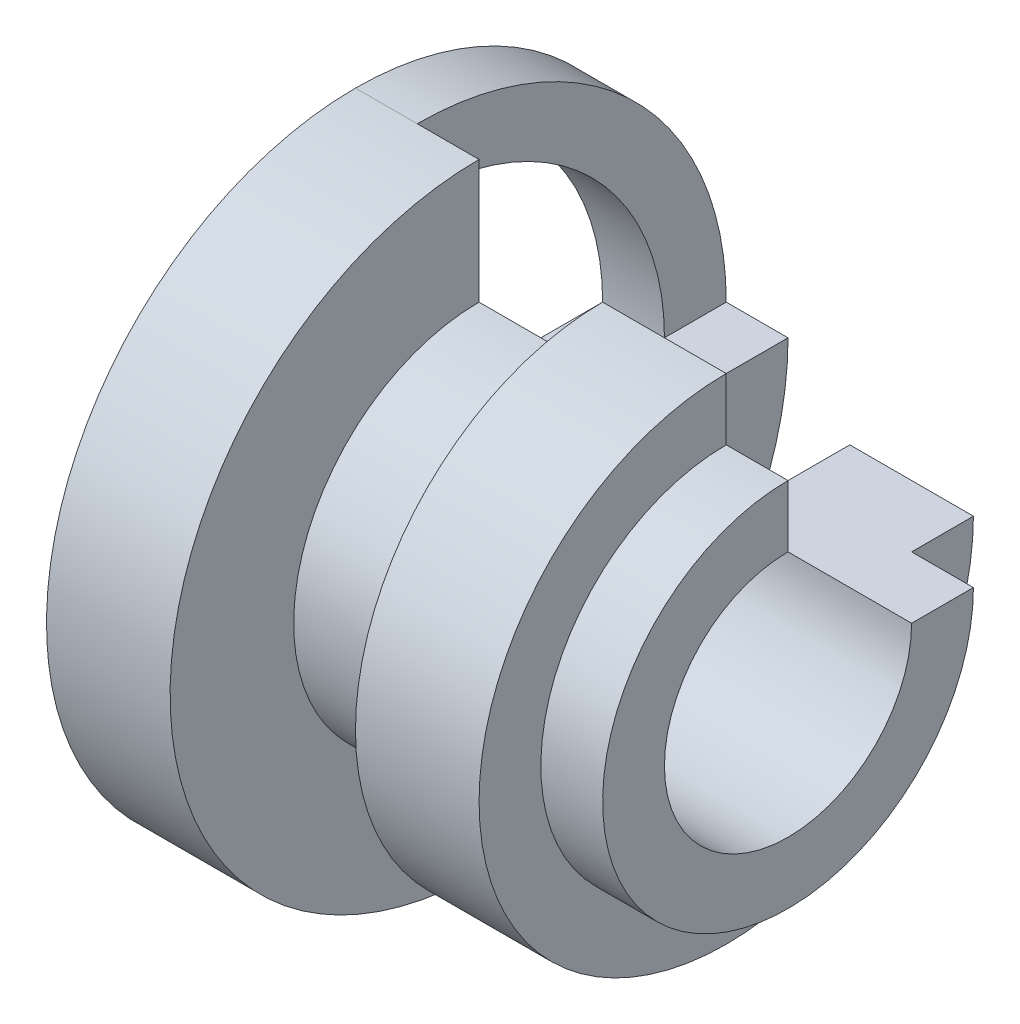
SolidWorks part; units mm, degrees
ref_plane "Front Plane" through (0, 0, 0) normal (0, 0, 1) x (1, 0, 0)
ref_plane "Top Plane" through (0, 0, 0) normal (0, 1, 0) x (1, 0, 0)
ref_plane "Right Plane" through (0, 0, 0) normal (1, 0, 0) x (0, 0, -1)
sketch "Sketch1" plane through (0, 0, 0) normal (0, 0, 1) x (1, 0, 0)
  line L0 (0, 5) -> (0, 2)
  line L1 (0, 2) -> (7, 2)
  line L2 (7, 2) -> (7, 3)
  line L3 (7, 3) -> (6, 3)
  line L4 (6, 3) -> (6, 4)
  line L5 (6, 4) -> (4, 4)
  line L6 (4, 4) -> (4, 3)
  line L7 (4, 3) -> (2, 3)
  line L8 (2, 3) -> (2, 5)
  line L9 (2, 5) -> (0, 5)
  line L10 (0, 0) -> (2.9136, 0) construction
  dimension "D1" = 2
  dimension "D2" = 3
  dimension "D3" = 2
  dimension "D4" = 2
  dimension "D5" = 2
  dimension "D6" = 1
  dimension "D7" = 1
  dimension "D8" = 2
  dimension "D9" = 1
revolve "Revolve1" add sketch "Sketch1" angle 270 about L10
sketch "Sketch2" plane through (0, 0, 0) normal (-1, 0, 0) x (0, 0, 1)
  line L0 (-3, 0) -> (-5, 0) construction
  line L1 (0, 3) -> (0, 5) construction
  line L2 (0, 5) -> (0, 4)
  line L3 (-4, 0) -> (-5, 0)
  arc A0 (0, 4) -> (-4, 0) centre (0, 0) ccw
  arc A1 (-5, 0) -> (0, 5) centre (0, 0) cw
  arc A2 (-5, 0) -> (0, 5) centre (0, 0) ccw construction
extrude "Boss-Extrude1" add sketch "Sketch2" against normal blind 1 separate body
